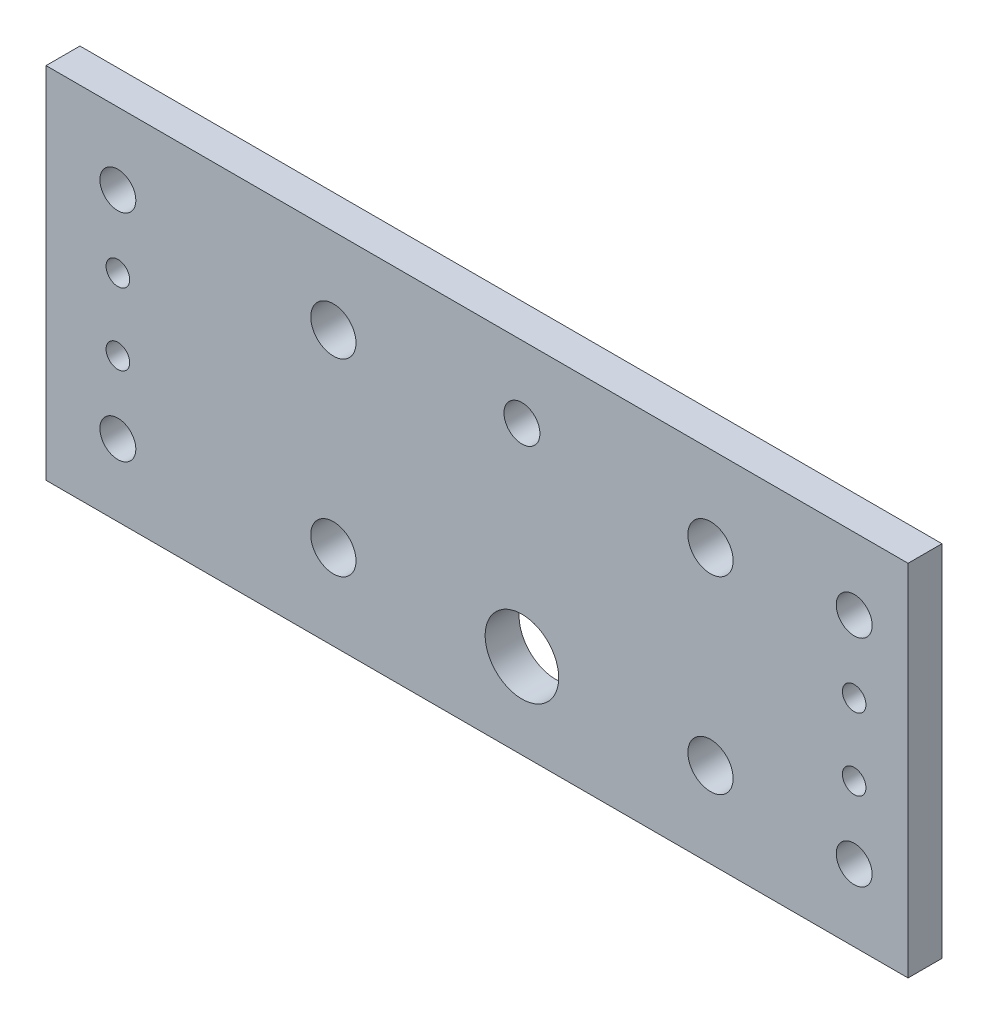
SolidWorks part; units mm, degrees
ref_plane "Front Plane" through (0, 0, 0) normal (0, 0, 1) x (1, 0, 0)
ref_plane "Top Plane" through (0, 0, 0) normal (0, 1, 0) x (1, 0, 0)
ref_plane "Right Plane" through (0, 0, 0) normal (1, 0, 0) x (0, 0, -1)
sketch "Sketch1" plane through (0, 0, 0) normal (0, 0, 1) x (1, 0, 0)
  line L0 (12.7, 63.5) -> (12.7, 0) construction
  line L1 (0, 0) -> (152.4, 0)
  line L2 (0, 0) -> (0, 63.5)
  line L3 (0, 63.5) -> (152.4, 63.5)
  line L4 (152.4, 0) -> (152.4, 63.5)
  line L5 (68.6375, 22.0749) -> (84.1375, 22.0749) construction
  line L6 (84.1375, 22.0749) -> (93.3875, 38.0964) construction
  line L7 (84.1375, 22.0749) -> (93.3875, 6.0534) construction
  line L8 (84.1375, 22.0749) -> (99.6375, 22.0749) construction
  line L9 (142.875, 63.5) -> (142.875, 0) construction
  line L10 (0, 31.75) -> (152.4, 31.75) construction
  circle A0 centre (84.1375, 15.0749) radius 6.5
  circle A1 centre (12.7, 38.1) radius 2.0828
  circle A2 centre (12.7, 25.4) radius 2.0828
  circle A3 centre (142.875, 38.1) radius 2.0828
  circle A4 centre (142.875, 25.4) radius 2.0828
  circle A9 centre (50.8, 48.4251) radius 4
  circle A10 centre (12.7, 50.8) radius 3.175
  circle A11 centre (12.7, 12.7) radius 3.175
  circle A12 centre (117.475, 48.4251) radius 4
  circle A13 centre (117.475, 15.0749) radius 4
  circle A14 centre (50.8, 15.0749) radius 4
  circle A27 centre (142.875, 50.8) radius 3.175
  circle A28 centre (142.875, 12.7) radius 3.175
  circle A29 centre (84.1375, 50.8) radius 3.175
  dimension "D3" = 13
  dimension "D7" = 4.1656
  dimension "D10" = 8
  dimension "D12" = 15.5
  dimension "D15" = 12.7
  dimension "D8" = 12.7
  dimension "D14" = 31
  dimension "D17" = 66.675
  dimension "D20" = 12.7
  dimension "D25" = 6.35
  dimension "D26" = 12.7
  dimension "D27" = 12.7
  dimension "D45" = 6.35
  dimension "D48" = 6.35
  dimension "D18" = 12.7
  dimension "D1" = 152.4
  dimension "D5" = 7
  dimension "D6" = 33.3375
  dimension "D9" = 120
  dimension "D11" = 60
  dimension "D13" = 63.5
  dimension "D16" = 33.3502
  dimension "D19" = 33.3502
  dimension "D23" = 12.7
  dimension "D28" = 50.8
  dimension "D44" = 25.4
  dimension "D46" = 12.7
  dimension "D47" = 12.7
extrude "Boss-Extrude1" add sketch "Sketch1" along normal blind 5.9944
